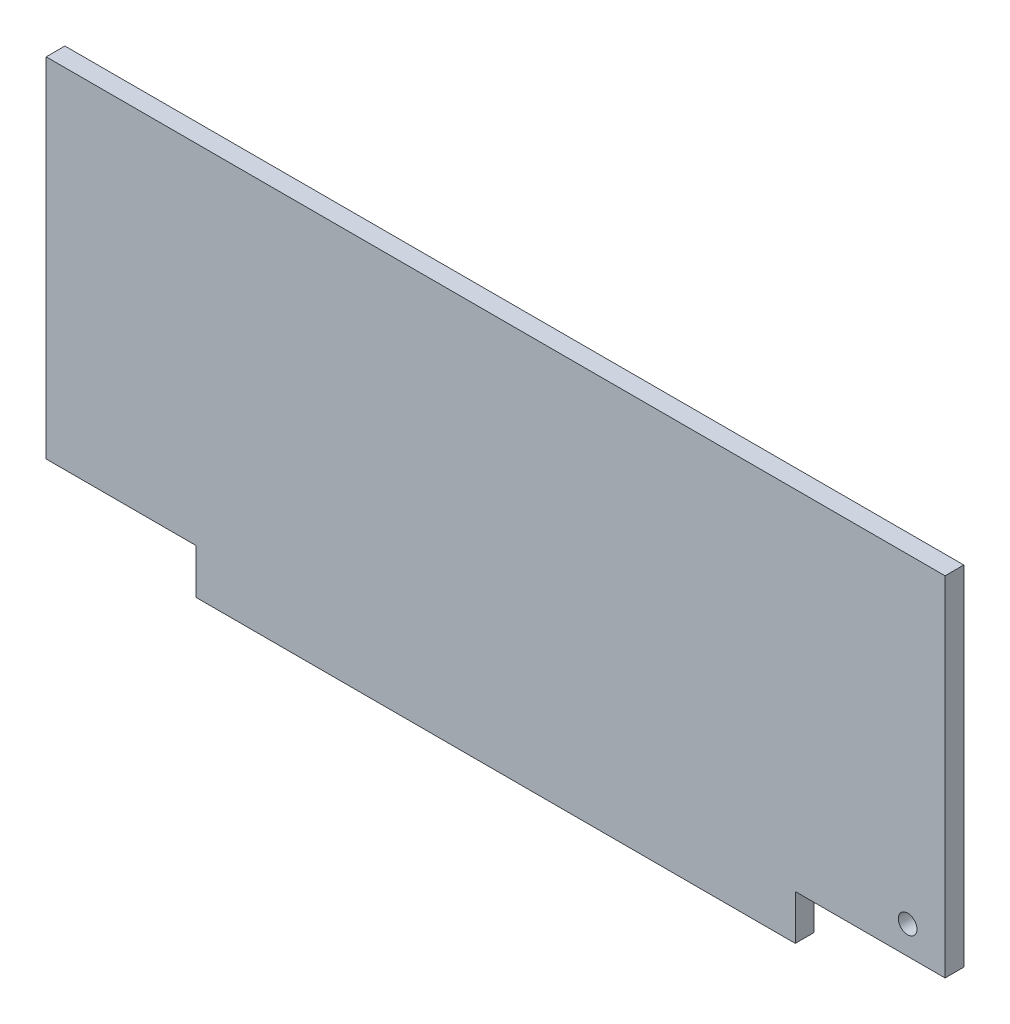
SolidWorks part; units mm, degrees
ref_plane "Plan de face" through (0, 0, 0) normal (0, 0, 1) x (1, 0, 0)
ref_plane "Plan de dessus" through (0, 0, 0) normal (0, 1, 0) x (1, 0, 0)
ref_plane "Plan de droite" through (0, 0, 0) normal (1, 0, 0) x (0, 0, -1)
sketch "Esquisse1" plane through (0, 0, 0) normal (0, 0, 1) x (1, 0, 0)
  line L1 (-290, 105) -> (190, 105)
  line L2 (-290, 105) -> (-290, -105)
  line L3 (-290, -105) -> (190, -105)
  line L4 (190, 105) -> (190, -105)
  dimension "D1" = 480
  dimension "D2" = 210
  dimension "D3" = 105
  dimension "D4" = 190
extrude "Boss.-Extru.1" add sketch "Esquisse1" along normal blind 10
sketch "Esquisse2" plane through (0, 0, 10) normal (0, 0, 1) x (1, 0, 0)
  line L1 (190, -105) -> (110, -105)
  line L2 (190, -105) -> (190, -81)
  line L3 (190, -81) -> (110, -81)
  line L4 (110, -105) -> (110, -81)
  line L5 (-290, -105) -> (-210, -105)
  line L6 (-290, -105) -> (-290, -81)
  line L7 (-290, -81) -> (-210, -81)
  line L8 (-210, -105) -> (-210, -81)
  dimension "D1" = 80
  dimension "D2" = 24
  dimension "D3" = 24
  dimension "D4" = 80
extrude "Enlèv. mat.-Extru.1" cut sketch "Esquisse2" against normal through all
sketch "Esquisse3" plane through (0, 0, 10) normal (0, 0, 1) x (1, 0, 0)
  line L0 (190, -81) -> (190, 105) construction
  line L2 (190, -81) -> (110, -81) construction
  circle A0 centre (170, -66) radius 5
  dimension "D1" = 20
  dimension "D2" = 15
  dimension "D3" = 10
extrude "Enlèv. mat.-Extru.2" cut sketch "Esquisse3" against normal through all
